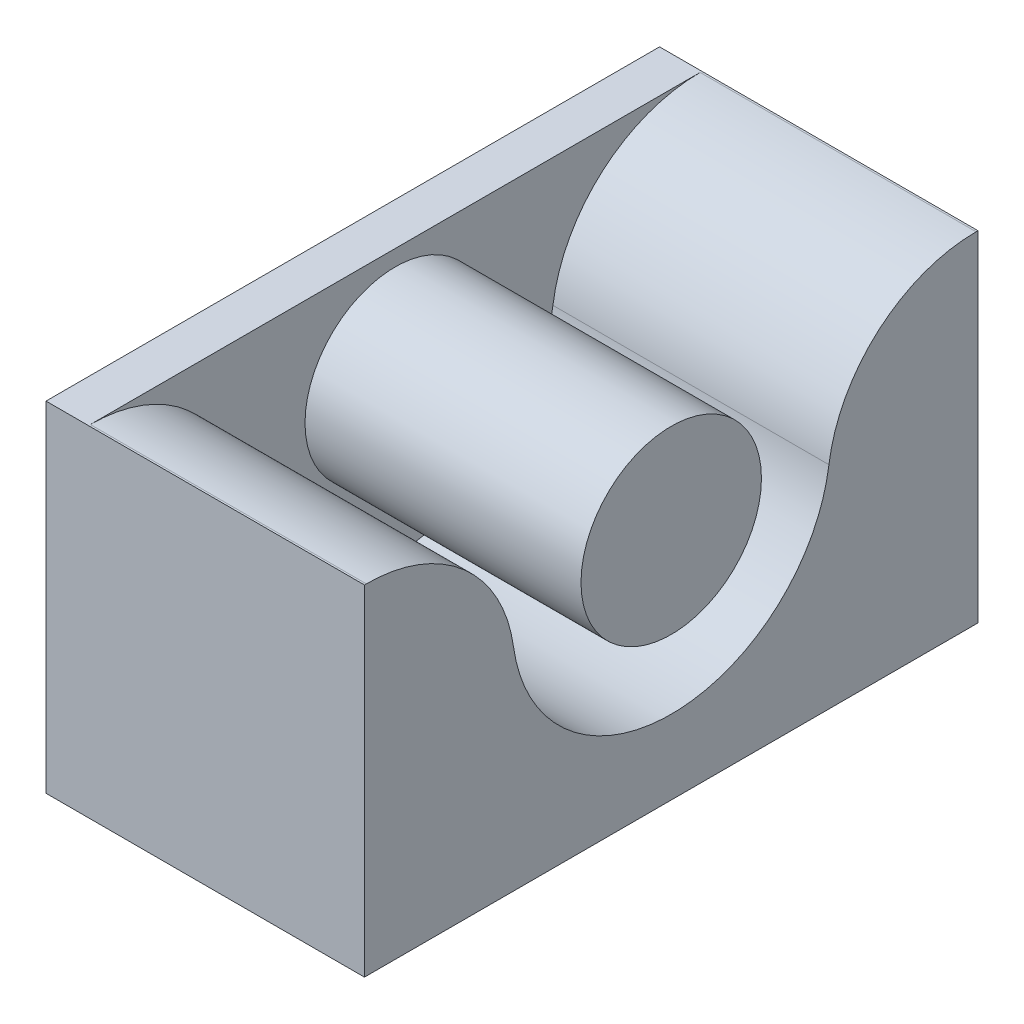
SolidWorks part; units mm, degrees
ref_plane "Alzado" through (0, 0, 0) normal (0, 0, 1) x (1, 0, 0)
ref_plane "Planta" through (0, 0, 0) normal (0, 1, 0) x (1, 0, 0)
ref_plane "Vista lateral" through (0, 0, 0) normal (1, 0, 0) x (0, 0, -1)
sketch "Croquis2" plane through (0, 0, 0) normal (1, 0, 0) x (0, 0, -1)
  line L0 (-14.45, 5) -> (-14.3614, 5)
  line L1 (-14.45, -11) -> (14.45, -11)
  line L2 (-14.45, 5) -> (-14.45, -11)
  line L3 (14.45, 5) -> (14.45, -11)
  line L4 (0, 0) -> (0, 2) construction
  line L5 (14.3614, 5) -> (14.45, 5)
  circle A0 centre (0, 0) radius 4.25
  arc A1 (-7.4283, -1.0345) -> (7.4283, -1.0345) centre (0, 0) ccw
  arc A2 (-14.3614, 5) -> (-7.4283, -1.0345) centre (-14.3614, -2) cw
  arc A3 (14.3614, 5) -> (7.4283, -1.0345) centre (14.3614, -2) ccw
  point P8 (0, 5)
  point P10 (0, -11)
  dimension "D1" = 8.5
  dimension "D2" = 15
  dimension "D5" = 7
  dimension "D3" = 5
  dimension "D4" = 11
  dimension "D6" = 28.9
  dimension "D7" = 2
extrude "Saliente-Extruir1" add sketch "Croquis2" along normal blind 15
sketch "Croquis3" plane through (0, 0, 0) normal (-1, 0, 0) x (0, 0, 1)
  line L1 (-14.45, 5) -> (14.45, 5)
  line L2 (-14.45, 5) -> (-14.45, -11)
  line L3 (-14.45, -11) -> (14.45, -11)
  line L4 (14.45, 5) -> (14.45, -11)
extrude "Saliente-Extruir2" add sketch "Croquis3" against normal blind 2
